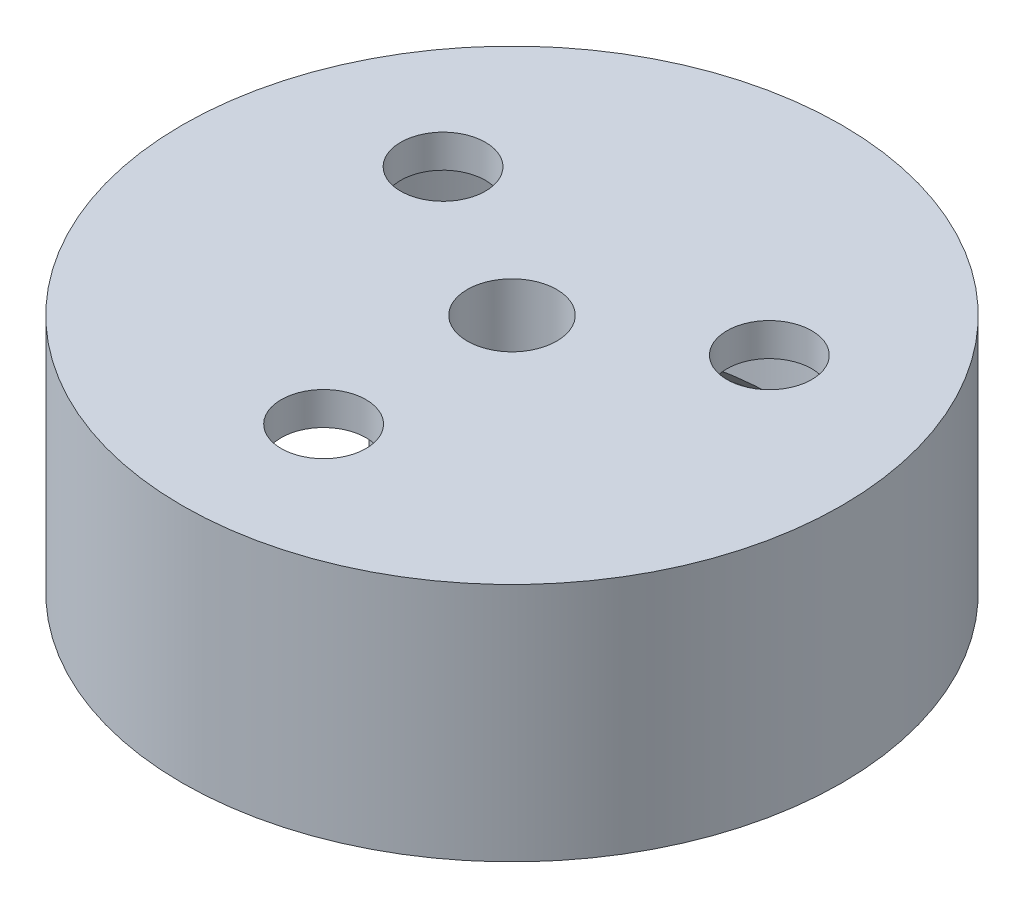
SolidWorks part; units mm, degrees
ref_plane "Спереди" through (0, 0, 0) normal (0, 0, 1) x (1, 0, 0)
ref_plane "Сверху" through (0, 0, 0) normal (0, 1, 0) x (1, 0, 0)
ref_plane "Справа" through (0, 0, 0) normal (1, 0, 0) x (0, 0, -1)
sketch "Эскиз1" plane through (0, 0, 0) normal (0, 1, 0) x (1, 0, 0)
  circle A0 centre (0, 0) radius 7
  dimension "D1" = 14
extrude "Бобышка-Вытянуть1" add sketch "Эскиз1" along normal blind 5.1
sketch "Эскиз4" plane through (0, 0, 0) normal (0, -1, 0) x (1, 0, 0)
  circle A0 centre (0, 0) radius 0.95
  dimension "D1" = 1.9
extrude "Вырез-Вытянуть2" cut sketch "Эскиз4" against normal blind 8 contours A0
sketch "Эскиз5" plane through (0, 0, 0) normal (0, -1, 0) x (-1, 0, 0)
  circle A0 centre (0, 0) radius 5.6
  circle A1 centre (0, 0) radius 7 construction
  circle A2 centre (0, 0) radius 2.15
  circle A3 centre (0, 0) radius 0.95 construction
  dimension "D1" = 1.4
  dimension "D2" = 1.2
extrude "Вырез-Вытянуть3" cut sketch "Эскиз5" against normal blind 4
sketch "Эскиз6" plane through (0, 0, 0) normal (0, -1, 0) x (1, 0, 0)
  line L0 (0, 0) -> (0, 7.0339) construction
  line L1 (-1.85, 6.3) -> (1.85, 6.3)
  line L2 (-1.85, 6.3) -> (-1.85, 5.5)
  line L3 (-1.85, 5.5) -> (1.85, 5.5)
  line L4 (1.85, 6.3) -> (1.85, 5.5)
  point P7 (0, 5.5)
  dimension "D1" = 0.8
  dimension "D2" = 3.7
  dimension "D3" = 5.5
extrude "Вырез-Вытянуть4" cut sketch "Эскиз6" against normal blind 4
chamfer "Фаска1" distance 0.8 angle 45 1 edges at (0, 0, -2.15)
chamfer "Фаска2" distance 0.8 angle 45 1 edges at (0, 0, -5.6)
sketch "Эскиз7" plane through (0, 4, 0) normal (0, -1, 0) x (1, 0, 0)
  circle A0 centre (0, 4) radius 1.5
  circle A1 centre (3.4641, -2) radius 1.5
  circle A2 centre (-3.4641, -2) radius 1.5
  point P10 (0, 0)
  dimension "D1" = 4
  dimension "D2" = 3
extrude "Вырез-Вытянуть5" cut sketch "Эскиз7" against normal blind 0.4
sketch "Эскиз8" plane through (0, 4, 0) normal (0, -1, 0) x (1, 0, 0)
  circle A0 centre (0, 4) radius 0.9
  circle A1 centre (3.4641, -2) radius 0.9
  circle A2 centre (-3.4641, -2) radius 0.9
  point P11 (0, 0)
  dimension "D1" = 3
extrude "Вырез-Вытянуть6" cut sketch "Эскиз8" against normal through all both and the other way through all
